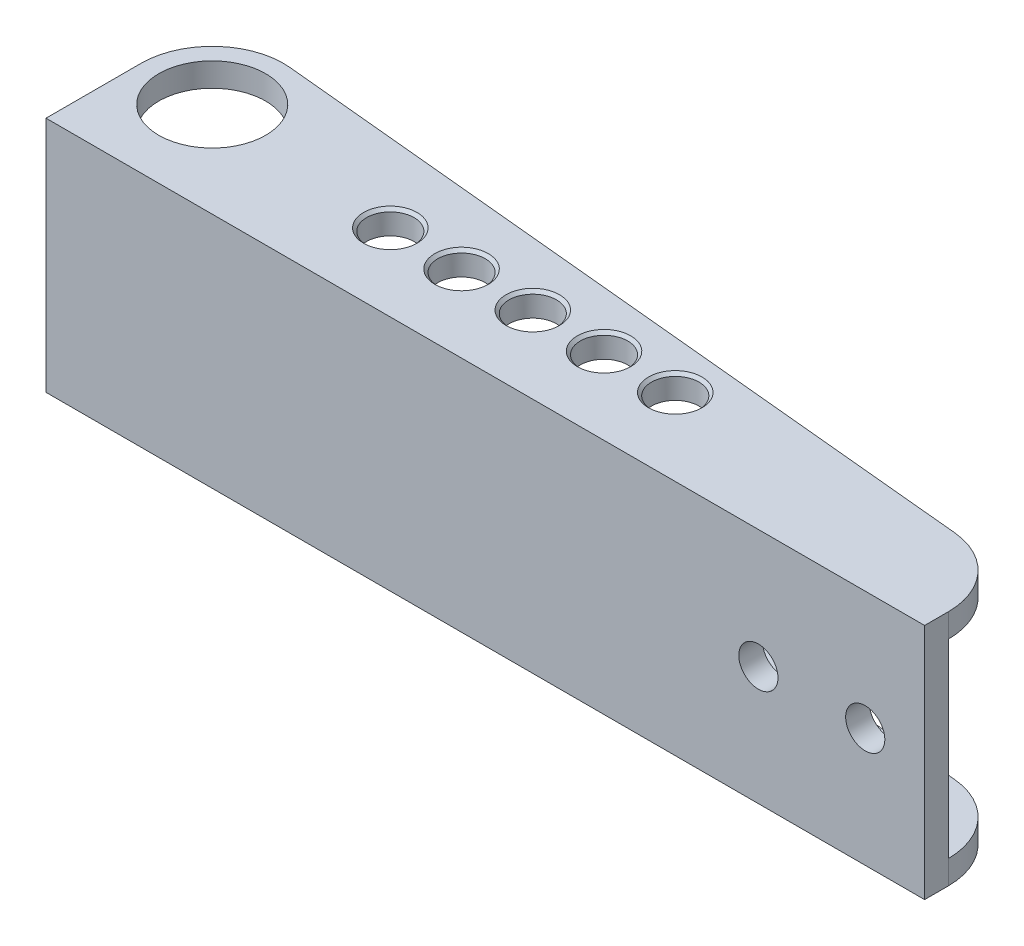
SolidWorks part; units mm, degrees
material "Alu 2017 (AU4G)"
ref_plane "Face" through (0, 0, 0) normal (0, 0, 1) x (1, 0, 0)
ref_plane "Dessus" through (0, 0, 0) normal (0, 1, 0) x (1, 0, 0)
ref_plane "Droite" through (0, 0, 0) normal (1, 0, 0) x (0, 0, -1)
sketch "Esquisse1" plane through (0, 0, 0) normal (0, 0, 1) x (1, 0, 0)
  line L1 (-74, 20) -> (74, 20)
  line L2 (-74, 20) -> (-74, -20)
  line L3 (-74, -20) -> (74, -20)
  line L4 (74, 20) -> (74, -20)
  line L5 (-74, 20) -> (74, -20) construction
  line L6 (-74, -20) -> (74, 20) construction
  point P0 (0, 0)
  dimension "D1" = 148
  dimension "D2" = 40
extrude "Boss.-Extru.1" add sketch "Esquisse1" along normal blind 30
sketch "Esquisse2" plane through (0, 20, 0) normal (0, 1, 0) x (1, 0, 0)
  line L0 (-74, -14) -> (-74, -30)
  line L1 (74, -30) -> (74, 0) construction
  line L2 (63.0503, -13.9489) -> (-60.8533, -2.0549)
  line L3 (-74, -30) -> (-74, 0) construction
  line L4 (-74, -30) -> (74, -30)
  line L5 (74, -26) -> (74, -30)
  arc A0 (-60.8533, -2.0549) -> (-74, -14) centre (-62, -14) ccw
  arc A1 (74, -26) -> (63.0503, -13.9489) centre (61.8935, -26) ccw
  point P17 (74, -15)
  point P18 (-62, -2)
  dimension "D1" = 16
  dimension "D2" = 28
  dimension "D3" = 4
extrude "Enlèv. mat.-Extru.1" cut sketch "Esquisse2" against normal through all flip side to cut
sketch "Esquisse3" plane through (-74, 0, 0) normal (-1, 0, 0) x (0, 0, 1)
  line L0 (2, 20) -> (2, -20) construction
  line L1 (2, 16) -> (26, 16)
  line L2 (2, 16) -> (2, -16)
  line L3 (2, -16) -> (26, -16)
  line L4 (26, 16) -> (26, -16)
  line L6 (0, 0) -> (26, 0) construction
  line L7 (30, 20) -> (30, -20) construction
  dimension "D1" = 32
  dimension "D2" = 4
extrude "Enlèv. mat.-Extru.3" cut sketch "Esquisse3" against normal through all
sketch "Esquisse4" plane through (0, 20, 0) normal (0, 1, 0) x (1, 0, 0)
  line L0 (74, -30) -> (-74, -30) construction
  line L1 (-74, -30) -> (-74, -14) construction
  circle A0 centre (-62, -14) radius 9
  circle A1 centre (-29, -17) radius 4
  circle A2 centre (-17, -17) radius 4
  circle A3 centre (-5, -17) radius 4
  circle A4 centre (7, -17) radius 4
  circle A5 centre (19, -17) radius 4
  dimension "D1" = 18
  dimension "D2" = 8
  dimension "D3" = 13
  dimension "D4" = 45
  dimension "D6" = 48
  dimension "D5" = 5
extrude "Enlèv. mat.-Extru.4" cut sketch "Esquisse4" against normal through all
chamfer "Chanfrein1" distance 0.5 angle 45 10 edges at (19, -20, 21) (7, -20, 21) (-5, -20, 21) (-17, -20, 21) (-29, -20, 21) (19, 20, 21) (7, 20, 21) (-5, 20, 21) (-17, 20, 21) (-29, 20, 21)
hole_wizard "Trou taraudé M31" positions "Esquisse6" profile "Esquisse5" tap size "M3" standard "ISO"
sketch "Esquisse6" plane through (0, -20, 0) normal (0, -1, 0) x (-1, 0, 0)
  line L0 (74, -30) -> (74, -14) construction
  line L1 (74, -30) -> (-74, -30) construction
  line L2 (23, -26) -> (35, -26) construction
  line L3 (29, -26) -> (29, -10) construction
  point P0 (29, -10)
  point P2 (23, -26)
  point P4 (35, -26)
  dimension "D1" = 12
  dimension "D2" = 39
  dimension "D3" = 4
  dimension "D4" = 20
sketch "Esquisse5" plane through (-29, -20, 10) normal (1, 0, 0) x (0, 0, -1)
  line L0 (0, 0) -> (0, 9.2511)
  line L1 (0, 9.2511) -> (1.25, 8.5)
  line L2 (1.25, 8.5) -> (1.25, 0.275)
  line L3 (1.25, 0.275) -> (1.525, 0)
  line L5 (1.525, 0) -> (0, 0)
  line L6 (-1.25, 0.275) -> (-1.525, 0) construction
  line L10 (0, 9.2511) -> (-1.25, 8.5) construction
  line L11 (0, -6.35) -> (0, 107.95) construction
  dimension "Diamètre du trou pour taraudage" = 2.5
  dimension "Profondeur du trou pour taraudage" = 8.5
  dimension "Diamètre du fraisage entrant" = 3.05
  dimension "Angle du fraisage entrant" = 90
  dimension "Angle de pointe" = 118
cosmetic thread "Filetage de perçage1" parameters "D1"=6, "D2"=3
cosmetic thread "Filetage de perçage2" parameters "D1"=6, "D2"=3
cosmetic thread "Filetage de perçage3" parameters "D1"=4, "D2"=3
hole_wizard "Dégagement M61" positions "Esquisse8" profile "Esquisse7" hole size "M6" standard "ISO" end condition through all
sketch "Esquisse8" plane through (0, 0, 30) normal (0, 0, 1) x (1, 0, 0)
  line L0 (74, -20) -> (74, 20) construction
  point P0 (46, 0)
  point P2 (64, 0)
  dimension "D1" = 10
  dimension "D2" = 18
sketch "Esquisse7" plane through (46, 0, 30) normal (1, 0, 0) x (0, -1, 0)
  line L0 (0, 0) -> (0, 28)
  line L1 (0, 28) -> (3.3, 28)
  line L2 (3.3, 28) -> (3.3, 0)
  line L5 (3.3, 0) -> (0, 0)
  line L11 (0, -6.35) -> (0, 107.95) construction
  dimension "Diamètre du perçage jusqu'au prochain" = 6.6
  dimension "Profondeur du perçage jusqu'au prochain" = 28
